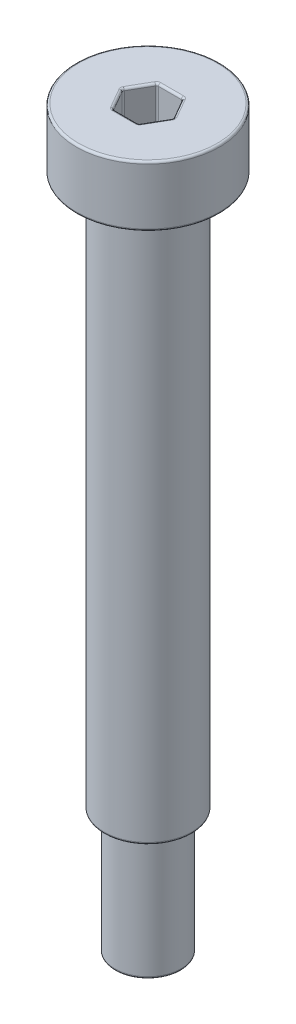
SolidWorks part; units mm, degrees
material "铸造碳钢"
ref_plane "Front" through (0, 0, 0) normal (0, 0, 1) x (1, 0, 0)
ref_plane "Top" through (0, 0, 0) normal (0, 1, 0) x (1, 0, 0)
ref_plane "Right" through (0, 0, 0) normal (1, 0, 0) x (0, 0, -1)
sketch "草图1" plane through (0, 0, 0) normal (0, 1, 0) x (1, 0, 0)
  circle A0 centre (0, 0) radius 3.99
  dimension "光杆直径" = 7.98
extrude "凸台-拉伸1" add sketch "草图1" against normal mid plane 50
sketch "草图2" plane through (0, 25, 0) normal (0, 1, 0) x (1, 0, 0)
  circle A0 centre (0, 0) radius 6.5
  dimension "头部直径" = 13
extrude "凸台-拉伸2" add sketch "草图2" along normal blind 5.5
sketch "草图3" plane through (0, 30.5, 0) normal (0, 1, 0) x (1, 0, 0)
  line L1 (2.3094, 0) -> (1.1547, 2)
  line L2 (1.1547, 2) -> (-1.1547, 2)
  line L3 (-1.1547, 2) -> (-2.3094, 0)
  line L4 (-2.3094, 0) -> (-1.1547, -2)
  line L5 (-1.1547, -2) -> (1.1547, -2)
  line L6 (1.1547, -2) -> (2.3094, 0)
  circle A0 centre (0, 0) radius 2 construction
  dimension "内六角对边" = 4
extrude "切除-拉伸1" cut sketch "草图3" against normal blind 3.3
sketch "草图4" plane through (0, -25, 0) normal (0, -1, 0) x (1, 0, 0)
  circle A0 centre (0, 0) radius 3
  dimension "螺丝直径" = 6
extrude "凸台-拉伸3" add sketch "草图4" along normal blind 11.25
fillet "圆角1" radius 0.2 23 edges at (0, 27.2, 2) (0, 30.5, 2) (1.1547, 28.85, 2) (1.7321, 27.2, 1) (1.7321, 30.5, 1) (2.3094, 28.85, 0) (1.7321, 27.2, -1) (1.7321, 30.5, -1) (-1.7321, 27.2, 1) (-1.1547, 28.85, 2) (-1.7321, 30.5, 1) (-1.7321, 27.2, -1) (-2.3094, 28.85, 0) (-1.7321, 30.5, -1) (1.1547, 28.85, -2) (0, 27.2, -2) (-1.1547, 28.85, -2) (0, 30.5, -2) (0, 25, 6.5) (0, 30.5, 6.5) (0, -25, 3.99) (0, -36.25, -3) (0, -25, -3)
move or copy body "实体-移动/复制1" [suppressed] bodies to move or copy 104
move or copy body "实体-移动/复制2" [suppressed] bodies to move or copy 104
move or copy body "实体-移动/复制3" [suppressed] bodies to move or copy 104
